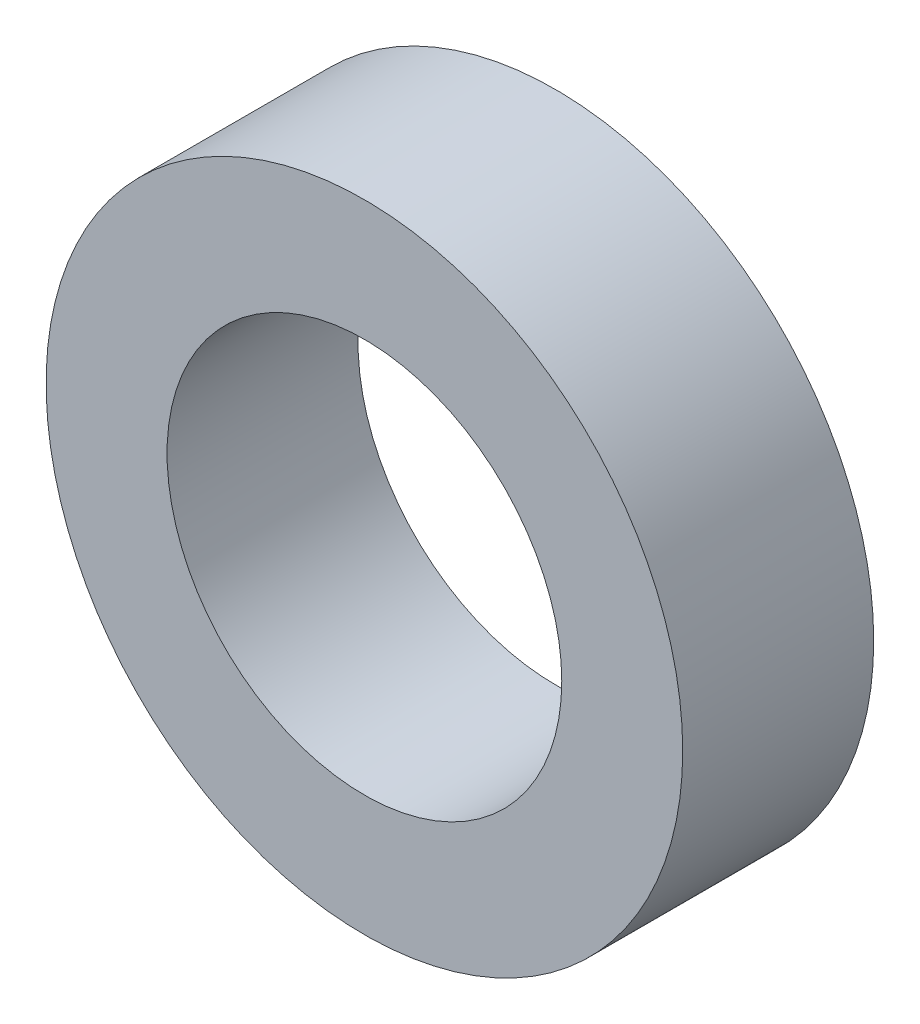
SolidWorks part; units mm, degrees
ref_plane "正面" through (0, 0, 0) normal (0, 0, 1) x (1, 0, 0)
ref_plane "平面" through (0, 0, 0) normal (0, 1, 0) x (1, 0, 0)
ref_plane "右側面" through (0, 0, 0) normal (1, 0, 0) x (0, 0, -1)
sketch "ｽｹｯﾁ1" plane through (0, 0, 0) normal (0, 0, 1) x (1, 0, 0)
  circle A0 centre (0, 0) radius 5
  circle A1 centre (0, 0) radius 3.1
  dimension "D1" = 10
  dimension "D2" = 6.2
extrude "ﾎﾞｽ - 押し出し3" add sketch "ｽｹｯﾁ1" along normal blind 3
